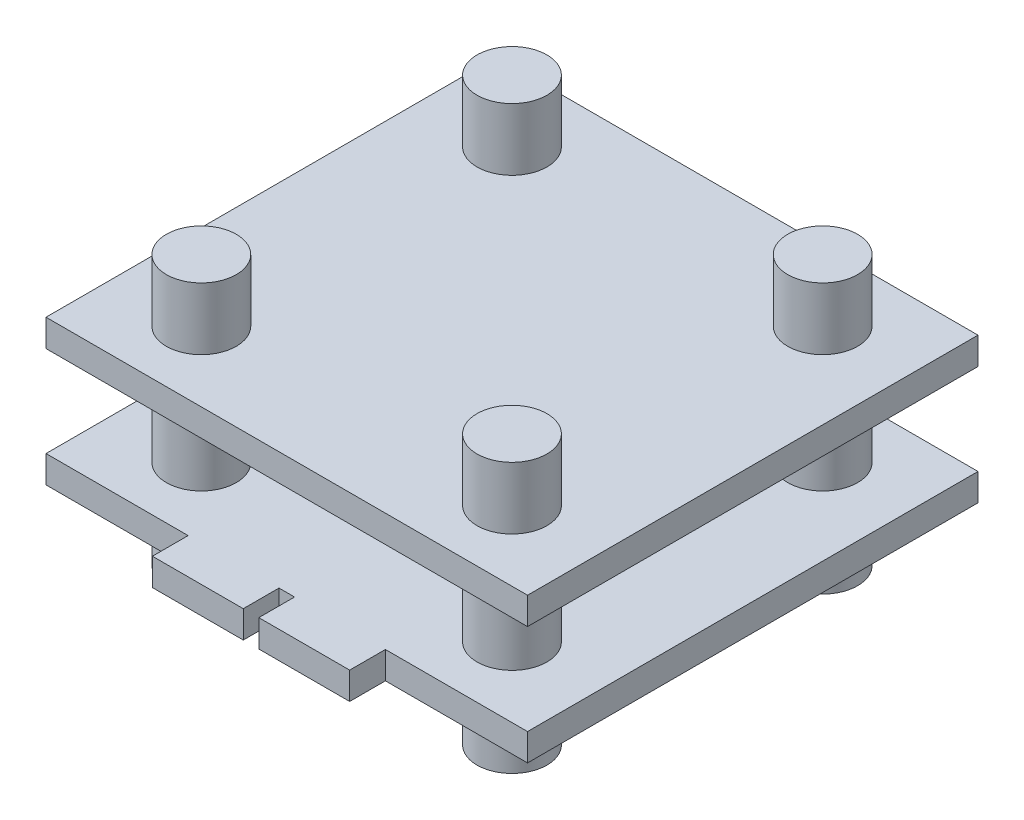
SolidWorks part; units mm, degrees
ref_plane "Front Plane" through (0, 0, 0) normal (0, 0, 1) x (1, 0, 0)
ref_plane "Top Plane" through (0, 0, 0) normal (0, 1, 0) x (1, 0, 0)
ref_plane "Right Plane" through (0, 0, 0) normal (1, 0, 0) x (0, 0, -1)
sketch "Sketch1" plane through (0, 0, 0) normal (0, 1, 0) x (1, 0, 0)
  line L1 (-15.5, 14.5) -> (15.5, 14.5)
  line L2 (-15.5, 14.5) -> (-15.5, -14.5)
  line L3 (-15.5, -14.5) -> (15.5, -14.5)
  line L4 (15.5, 14.5) -> (15.5, -14.5)
  line L5 (-15.5, 14.5) -> (15.5, -14.5) construction
  line L6 (-15.5, -14.5) -> (15.5, 14.5) construction
  point P0 (0, 0)
  dimension "D1" = 29
  dimension "D2" = 31
extrude "Boss-Extrude1" add sketch "Sketch1" along normal blind 1.75
sketch "Sketch2" plane through (0, 1.75, 0) normal (0, 1, 0) x (1, 0, 0)
  line L0 (0, 14.5) -> (0, -14.5) construction
  line L1 (15.5, 14.5) -> (-15.5, 14.5) construction
  line L2 (-15.5, -14.5) -> (15.5, -14.5) construction
  line L3 (-15.5, 0) -> (15.5, 0) construction
  line L4 (-15.5, 14.5) -> (-15.5, -14.5) construction
  line L5 (15.5, -14.5) -> (15.5, 14.5) construction
  circle A0 centre (-10, 10) radius 2.25
  circle A1 centre (10, 10) radius 2.25
  circle A2 centre (10, -10) radius 2.25
  circle A3 centre (-10, -10) radius 2.25
  dimension "D1" = 4.5
  dimension "D2" = 20
  dimension "D3" = 20
extrude "Boss-Extrude2" add sketch "Sketch2" along normal blind 5.85
sketch "Sketch3" plane through (0, 7.6, 0) normal (0, 1, 0) x (1, 0, 0)
  line L4 (15.5, -14.5) -> (15.5, 14.5)
  line L5 (15.5, 14.5) -> (-15.5, 14.5)
  line L6 (-15.5, 14.5) -> (-15.5, -14.5)
  line L7 (-15.5, -14.5) -> (15.5, -14.5)
  line L8 (15.5, -14.5) -> (15.5, 14.5)
  line L9 (15.5, 14.5) -> (-15.5, 14.5)
  line L10 (-15.5, 14.5) -> (-15.5, -14.5)
  line L11 (-15.5, -14.5) -> (15.5, -14.5)
  dimension "D1" = 0
extrude "Boss-Extrude3" add sketch "Sketch3" along normal blind 1.75
sketch "Sketch4" plane through (0, 9.35, 0) normal (0, 1, 0) x (1, 0, 0)
  circle A0 centre (-10, 10) radius 2.25 construction
  circle A1 centre (10, 10) radius 2.25 construction
  circle A2 centre (10, -10) radius 2.25 construction
  circle A3 centre (-10, -10) radius 2.25 construction
  circle A4 centre (-10, 10) radius 2.25
  circle A5 centre (10, 10) radius 2.25
  circle A6 centre (10, -10) radius 2.25
  circle A7 centre (-10, -10) radius 2.25
extrude "Boss-Extrude4" add sketch "Sketch4" along normal blind 4
sketch "Sketch5" plane through (0, 0, 0) normal (0, -1, 0) x (1, 0, 0)
  circle A0 centre (10, 10) radius 2.25 construction
  circle A1 centre (10, -10) radius 2.25 construction
  circle A2 centre (-10, -10) radius 2.25 construction
  circle A3 centre (-10, 10) radius 2.25 construction
  circle A4 centre (10, 10) radius 2.25
  circle A5 centre (10, -10) radius 2.25
  circle A6 centre (-10, -10) radius 2.25
  circle A7 centre (-10, 10) radius 2.25
extrude "Boss-Extrude5" add sketch "Sketch5" along normal blind 4
sketch "Sketch6" plane through (0, 0, 0) normal (0, -1, 0) x (1, 0, 0)
  line L0 (0, 14.5) -> (0, -14.5) construction
  line L1 (-15.5, 14.5) -> (15.5, 14.5) construction
  line L2 (15.5, -14.5) -> (-15.5, -14.5) construction
  line L3 (0.5, 14.5) -> (6.35, 14.5)
  line L4 (-0.5, 14.5) -> (-6.35, 14.5)
  line L5 (-0.5, 14.5) -> (-0.5, 16.8)
  line L6 (-0.5, 16.8) -> (-6.35, 16.8)
  line L7 (-6.35, 14.5) -> (-6.35, 16.8)
  line L8 (6.35, 14.5) -> (6.35, 16.8)
  line L9 (0.5, 16.8) -> (6.35, 16.8)
  line L10 (0.5, 14.5) -> (0.5, 16.8)
  point P14 (0.5, 15.65)
  dimension "D1" = 5.85
  dimension "D2" = 1
  dimension "D3" = 2.3
extrude "Boss-Extrude6" add sketch "Sketch6" against normal up to surface (1.75 mm away) up to face at (-10, 1.75, 7.75)
